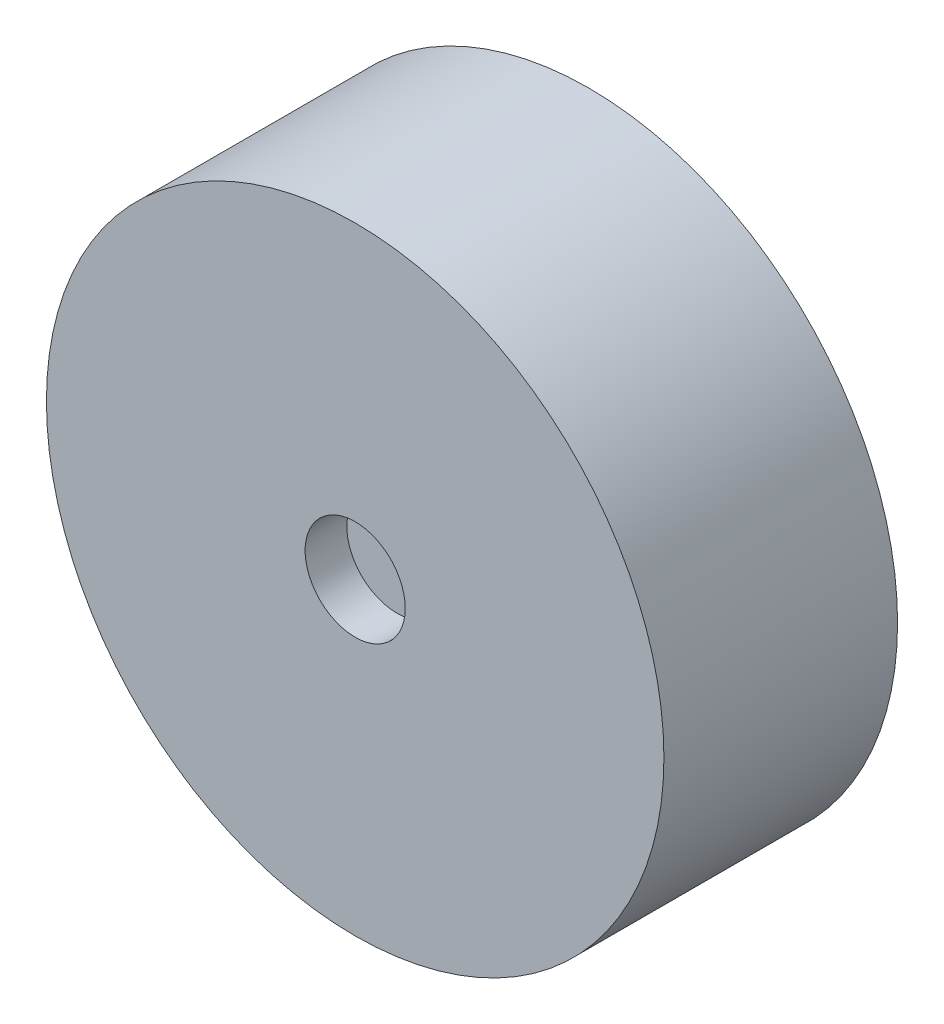
SolidWorks part; units mm, degrees
ref_plane "前视基准面" through (0, 0, 0) normal (0, 0, 1) x (1, 0, 0)
ref_plane "上视基准面" through (0, 0, 0) normal (0, 1, 0) x (1, 0, 0)
ref_plane "右视基准面" through (0, 0, 0) normal (1, 0, 0) x (0, 0, -1)
sketch "草图1" plane through (0, 0, 0) normal (0, 0, 1) x (1, 0, 0)
  circle A0 centre (0, 0) radius 18.5
  dimension "D1" = 37
extrude "凸台-拉伸1" add sketch "草图1" along normal blind 14
sketch "草图2" plane through (0, 0, 0) normal (0, 0, -1) x (-1, 0, 0)
  circle A0 centre (0, 0) radius 3
  dimension "D1" = 6
extrude "切除-拉伸1" cut sketch "草图2" against normal blind 2.5
sketch "草图3" plane through (0, 0, 14) normal (0, 0, 1) x (1, 0, 0)
  circle A0 centre (0, 0) radius 3
  dimension "D1" = 6
extrude "切除-拉伸2" cut sketch "草图3" against normal blind 2.5
